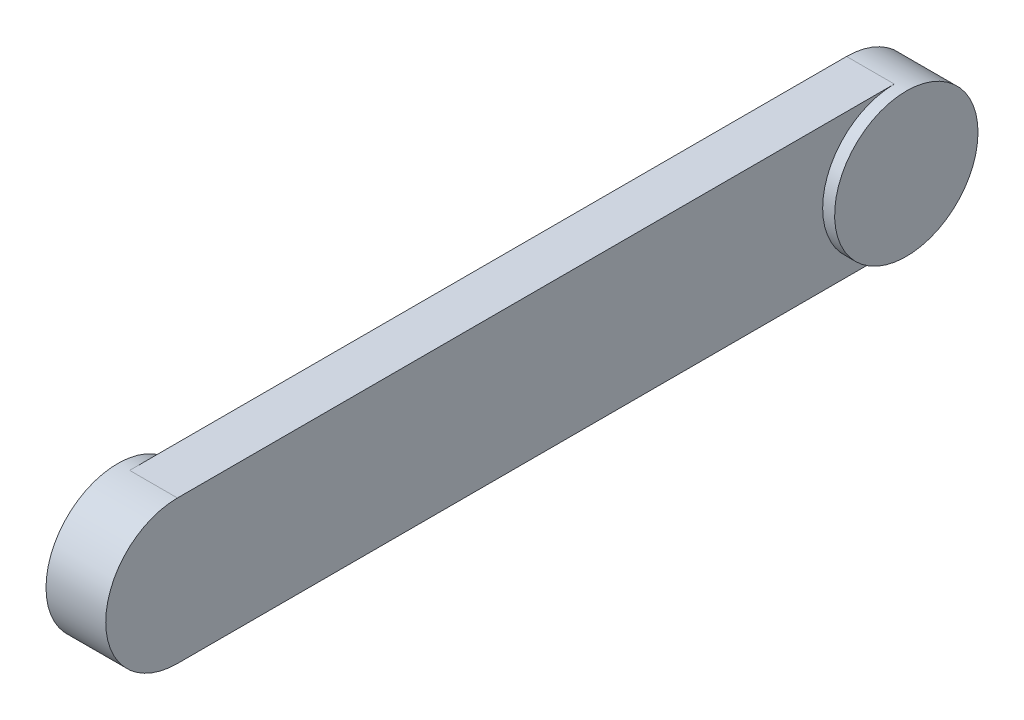
SolidWorks part; units mm, degrees
ref_plane "前视基准面" through (0, 0, 0) normal (0, 0, 1) x (1, 0, 0)
ref_plane "上视基准面" through (0, 0, 0) normal (0, 1, 0) x (1, 0, 0)
ref_plane "右视基准面" through (0, 0, 0) normal (1, 0, 0) x (0, 0, -1)
sketch "草图1" plane through (0, 0, 0) normal (1, 0, 0) x (0, 0, -1)
  line L0 (0, 30) -> (300, 30)
  line L1 (0, -30) -> (300, -30)
  arc A1 (300, -30) -> (300, 30) centre (300, 0) ccw
  arc A2 (0, 30) -> (0, -30) centre (0, 0) ccw
extrude "凸台-拉伸1" add sketch "草图1" along normal blind 20
sketch "草图2" plane through (20, 0, 0) normal (1, 0, 0) x (0, 0, -1)
  circle A0 centre (300, 0) radius 30
extrude "凸台-拉伸2" add sketch "草图2" along normal blind 5
sketch "草图3" plane through (0, 0, 0) normal (-1, 0, 0) x (0, 0, 1)
  circle A0 centre (0, 0) radius 30
extrude "凸台-拉伸3" add sketch "草图3" along normal blind 5
